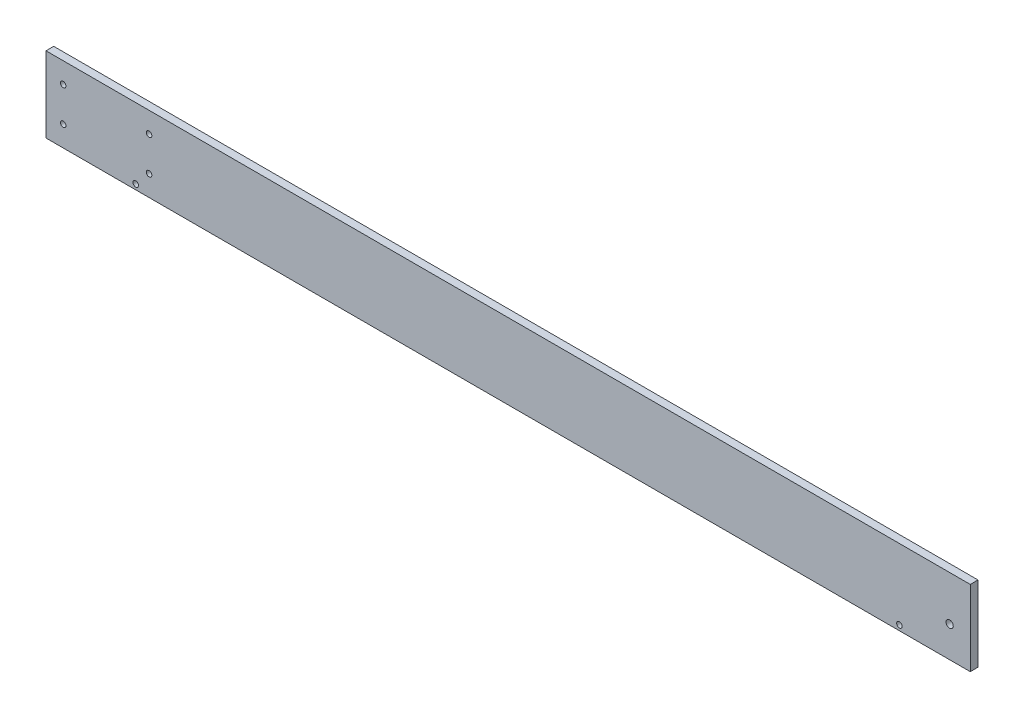
SolidWorks part; units mm, degrees
ref_plane "Front Plane" through (0, 0, 0) normal (0, 0, 1) x (1, 0, 0)
ref_plane "Top Plane" through (0, 0, 0) normal (0, 1, 0) x (1, 0, 0)
ref_plane "Right Plane" through (0, 0, 0) normal (1, 0, 0) x (0, 0, -1)
sketch "Sketch1" plane through (0, 0, 0) normal (0, 0, 1) x (1, 0, 0)
  line L0 (-269, 0) -> (-154.8681, 0) construction
  line L1 (-269, -22) -> (269, -22)
  line L2 (-269, -22) -> (-269, 22)
  line L3 (-269, 22) -> (269, 22)
  line L4 (269, -22) -> (269, 22)
  line L5 (-269, -22) -> (269, 22) construction
  line L6 (-269, 22) -> (269, -22) construction
  line L7 (-269, 22) -> (-269, 39) construction
  circle A0 centre (257, -4) radius 2.1 construction
  circle A1 centre (257, -4) radius 2.1
  circle A2 centre (-259, 10) radius 1.6
  circle A3 centre (-209, 10) radius 1.6
  circle A6 centre (-209, -10) radius 1.6
  circle A9 centre (-259, -10) radius 1.6
  circle A10 centre (227.75, -19) radius 1.6 construction
  circle A11 centre (227.75, -19) radius 1.6
  circle A12 centre (-216.75, -19) radius 1.6 construction
  circle A13 centre (-216.75, -19) radius 1.6
  point P0 (0, 0)
  dimension "D3" = 3.2
  dimension "D1" = 538
  dimension "D2" = 44
  dimension "D4" = 10
  dimension "D5" = 10
  dimension "D6" = 2
  dimension "D7" = 2
extrude "Boss-Extrude1" add sketch "Sketch1" along normal blind 4.5
